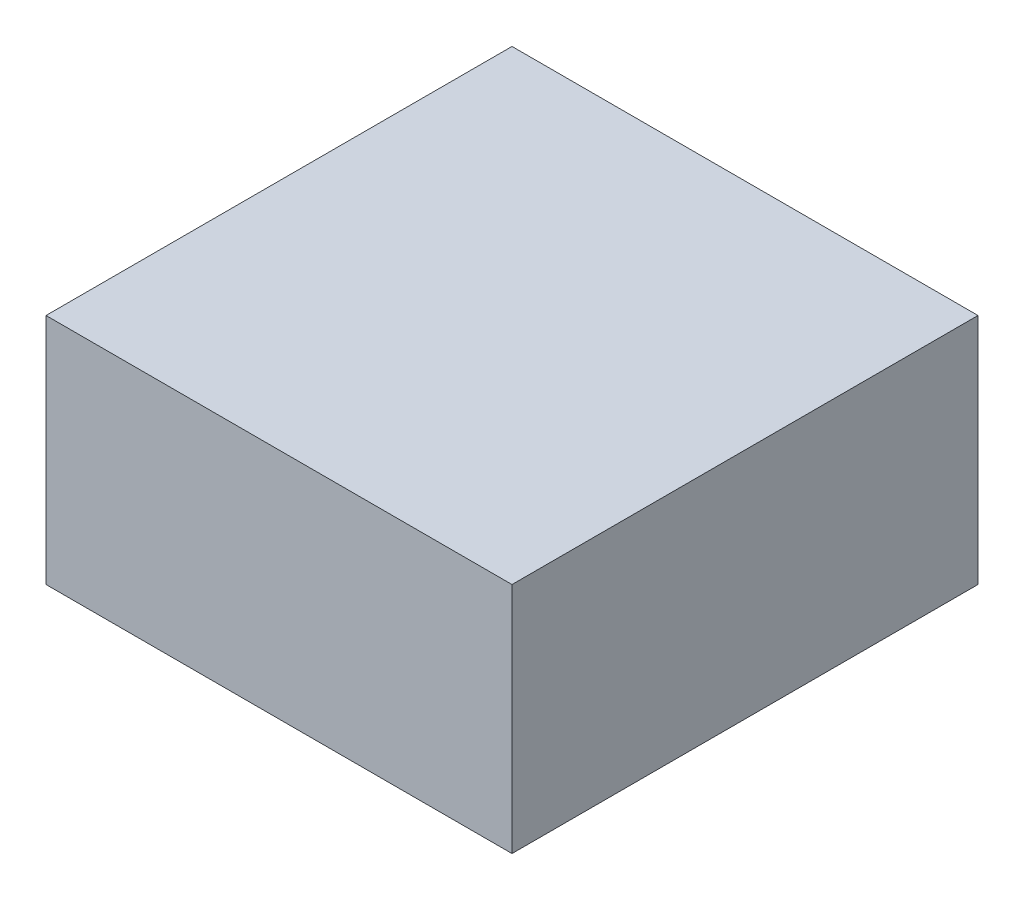
SolidWorks part; units mm, degrees
ref_plane "Front" through (0, 0, 0) normal (0, 0, 1) x (1, 0, 0)
ref_plane "Top" through (0, 0, 0) normal (0, 1, 0) x (1, 0, 0)
ref_plane "Right" through (0, 0, 0) normal (1, 0, 0) x (0, 0, -1)
sketch "Sketch1" plane through (0, 0, 0) normal (0, 0, 1) x (1, 0, 0)
  line L1 (-20, 10) -> (20, 10)
  line L2 (-20, 10) -> (-20, -10)
  line L3 (-20, -10) -> (20, -10)
  line L4 (20, 10) -> (20, -10)
  line L5 (-20, 10) -> (20, -10) construction
  line L6 (-20, -10) -> (20, 10) construction
  point P0 (0, 0)
  dimension "D1" = 40
  dimension "D2" = 20
extrude "Boss-Extrude1" add sketch "Sketch1" along normal blind 40
